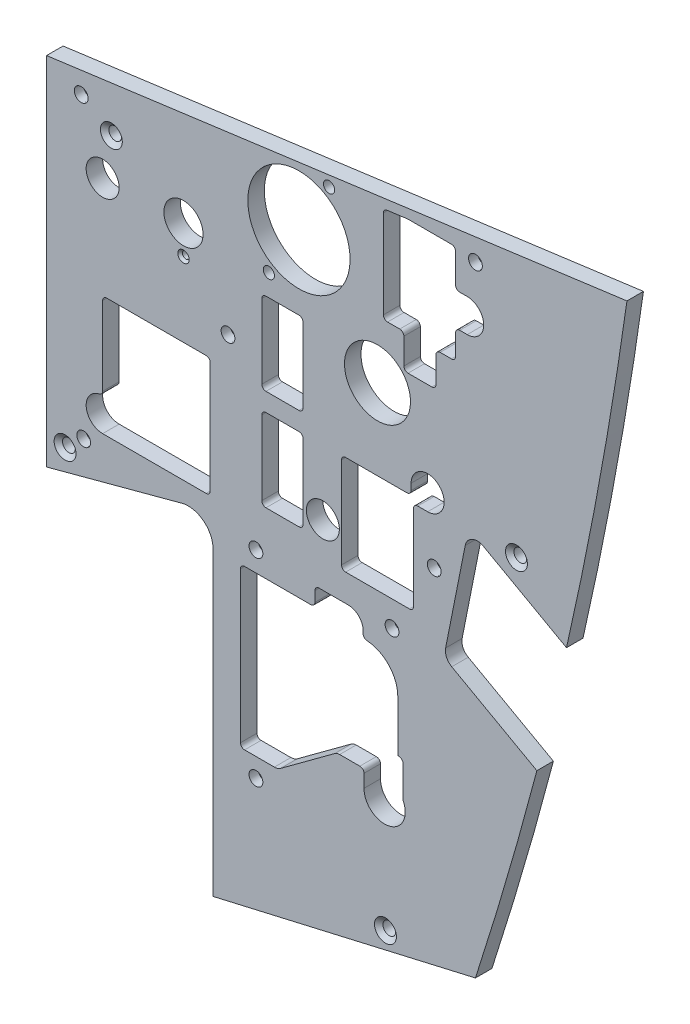
SolidWorks part; units mm, degrees
material "Acrylic (Medium-high impact)"
ref_plane "Front" through (0, 0, 0) normal (0, 0, 1) x (1, 0, 0)
ref_plane "Top" through (0, 0, 0) normal (0, 1, 0) x (1, 0, 0)
ref_plane "Right" through (0, 0, 0) normal (1, 0, 0) x (0, 0, -1)
sketch "Sketch1" plane through (0, 0, 0) normal (0, 0, 1) x (1, 0, 0)
  line L1 (3141.7988, 1080.7682) -> (3141.7988, 1063.3184)
  line L8 (3063.005, 1044.5596) -> (3063.005, 919.1617)
  line L9 (3063.005, 919.1617) -> (3164.2685, 942.5317)
  line L10 (3192.1789, 1037.6972) -> (3156.0776, 1057.8011)
  line L11 (3156.0776, 1057.8011) -> (3161.7423, 1086.3009)
  line L12 (3161.7423, 1086.3009) -> (3199.0539, 1065.5229)
  line L13 (3225.6026, 1207.3158) -> (2998.9238, 1176.9707)
  line L14 (2998.9238, 1176.9707) -> (2998.9238, 1039.8023)
  line L15 (2998.9238, 1039.8023) -> (3051.0147, 1053.76)
  line L16 (3063.005, 1044.5596) -> (3063.005, 919.1617)
  line L17 (3063.005, 919.1617) -> (3164.2685, 942.5317)
  line L18 (3192.1789, 1037.6972) -> (3156.0776, 1057.8011)
  line L19 (3156.0776, 1057.8011) -> (3161.7423, 1086.3009)
  line L20 (3161.7423, 1086.3009) -> (3199.0539, 1065.5229)
  line L21 (3225.6026, 1207.3158) -> (2998.9238, 1176.9707)
  line L22 (2998.9238, 1176.9707) -> (2998.9238, 1039.8023)
  line L23 (2998.9238, 1039.8023) -> (3051.0147, 1053.76)
  line L28 (3086.0872, 970.3576) -> (3119.75, 970.3576)
  line L29 (3085.0712, 977.1044) -> (3085.0712, 971.3736)
  line L30 (3074.5778, 981.8669) -> (3080.3087, 981.8669)
  line L31 (3073.5618, 1046.7322) -> (3073.5618, 982.8829)
  line L32 (3079.515, 1047.7482) -> (3074.5778, 1047.7482)
  line L33 (3084.2775, 1057.4478) -> (3084.2775, 1052.5107)
  line L34 (3125.3302, 1058.4638) -> (3085.2935, 1058.4638)
  line L35 (3126.3462, 1051.7169) -> (3126.3462, 1057.4478)
  line L36 (3136.8396, 1046.9544) -> (3131.1087, 1046.9544)
  line L37 (3137.8556, 988.4632) -> (3137.8556, 1045.9384)
  line L38 (3120.4684, 970.6551) -> (3137.558, 987.7447)
  line L39 (3086.0872, 970.3576) -> (3119.75, 970.3576)
  line L40 (3085.0712, 977.1044) -> (3085.0712, 971.3736)
  line L41 (3003.6862, 1145.6652) -> (3003.6863, 1063.3057)
  line L42 (3005.9087, 1147.2527) -> (3005.2737, 1147.2527)
  line L43 (3007.4962, 1162.696) -> (3007.4962, 1148.8402)
  line L44 (3012.2588, 1164.2835) -> (3009.0837, 1164.2835)
  line L45 (3018.6087, 1174.8809) -> (3018.6087, 1170.6476)
  line L46 (3036.8683, 1178.677) -> (3019.989, 1176.4548)
  line L47 (3031.8897, 1148.0185) -> (3038.6211, 1176.7408)
  line L48 (3037.8345, 1125.9265) -> (3031.9301, 1146.4148)
  line L49 (3060.8362, 1123.6307) -> (3040.8854, 1123.6307)
  line L50 (3062.4237, 1118.8682) -> (3062.4237, 1122.0432)
  line L51 (3075.1237, 1138.2357) -> (3075.1237, 1118.8682)
  line L52 (3108.2566, 1139.8232) -> (3076.7112, 1139.8232)
  line L53 (3126.5658, 1189.5696) -> (3111.2792, 1142.0263)
  line L54 (3155.879, 1194.3451) -> (3127.8699, 1190.6576)
  line L55 (3157.6737, 1190.6137) -> (3157.6737, 1192.7711)
  line L56 (3167.1987, 1184.2637) -> (3164.0237, 1184.2637)
  line L57 (3168.7862, 1148.0782) -> (3168.7862, 1182.6762)
  line L58 (3162.4362, 1146.4907) -> (3167.1987, 1146.4907)
  line L59 (3152.938, 1123.7744) -> (3156.193, 1141.3003)
  line L60 (3152.9113, 1088.7057) -> (3152.9113, 1123.4845)
  line L61 (3148.1488, 1087.1182) -> (3151.3238, 1087.1182)
  line L62 (3151.3238, 1074.4182) -> (3148.1488, 1074.4182)
  line L63 (3152.9113, 1063.3057) -> (3152.9113, 1072.8307)
  line L64 (3005.2738, 1061.7182) -> (3151.3238, 1061.7182)
  line L65 (3003.6862, 1145.6652) -> (3003.6863, 1063.3057)
  line L66 (3005.9087, 1147.2527) -> (3005.2737, 1147.2527)
  line L67 (3007.4962, 1162.696) -> (3007.4962, 1148.8402)
  line L68 (3012.2588, 1164.2835) -> (3009.0837, 1164.2835)
  line L69 (3018.6087, 1174.8809) -> (3018.6087, 1170.6476)
  line L70 (3036.8683, 1178.677) -> (3019.989, 1176.4548)
  line L71 (3031.8897, 1148.0185) -> (3038.6211, 1176.7408)
  line L72 (3037.8345, 1125.9265) -> (3031.9301, 1146.4148)
  line L73 (3060.8362, 1123.6307) -> (3040.8854, 1123.6307)
  line L74 (3062.4237, 1118.8682) -> (3062.4237, 1122.0432)
  line L75 (3075.1237, 1138.2357) -> (3075.1237, 1118.8682)
  line L76 (3108.2566, 1139.8232) -> (3076.7112, 1139.8232)
  line L77 (3126.5658, 1189.5696) -> (3111.2792, 1142.0263)
  line L78 (3155.879, 1194.3451) -> (3127.8699, 1190.6576)
  line L79 (3157.6737, 1190.6137) -> (3157.6737, 1192.7711)
  line L80 (3167.1987, 1184.2637) -> (3164.0237, 1184.2637)
  line L81 (3168.7862, 1148.0782) -> (3168.7862, 1182.6762)
  line L82 (3162.4362, 1146.4907) -> (3167.1987, 1146.4907)
  line L83 (3152.938, 1123.7744) -> (3156.193, 1141.3003)
  line L84 (3152.9113, 1088.7057) -> (3152.9113, 1123.4845)
  line L85 (3148.1488, 1087.1182) -> (3151.3238, 1087.1182)
  line L88 (3005.2738, 1061.7182) -> (3140.1986, 1061.7182)
  line L89 (3074.5778, 981.8669) -> (3080.3087, 981.8669)
  line L90 (3073.5618, 1046.7322) -> (3073.5618, 982.8829)
  line L91 (3079.515, 1047.7482) -> (3074.5778, 1047.7482)
  line L92 (3084.2775, 1057.4478) -> (3084.2775, 1052.5107)
  line L93 (3125.3302, 1058.4638) -> (3085.2935, 1058.4638)
  line L94 (3126.3462, 1051.7169) -> (3126.3462, 1057.4478)
  line L95 (3136.8396, 1046.9544) -> (3131.1087, 1046.9544)
  line L96 (3137.8556, 988.4632) -> (3137.8556, 1045.9384)
  line L97 (3120.4684, 970.6551) -> (3137.558, 987.7447)
  arc A0 (3141.7988, 1063.3184) -> (3140.1986, 1061.7182) centre (3140.1986, 1063.3184) cw
  arc A1 (3063.005, 1044.5596) -> (3051.0147, 1053.76) centre (3053.48, 1044.5596) ccw
  arc A2 (3063.005, 1044.5596) -> (3051.0147, 1053.76) centre (3053.48, 1044.5596) ccw
  arc A13 (3119.75, 970.3576) -> (3120.4684, 970.6551) centre (3119.75, 971.3736) ccw
  arc A14 (3085.0712, 971.3736) -> (3086.0872, 970.3576) centre (3086.0872, 971.3736) ccw
  arc A15 (3085.0712, 977.1044) -> (3080.3087, 981.8669) centre (3080.3087, 977.1044) ccw
  arc A16 (3073.5618, 982.8829) -> (3074.5778, 981.8669) centre (3074.5778, 982.8829) ccw
  arc A17 (3074.5778, 1047.7482) -> (3073.5618, 1046.7322) centre (3074.5778, 1046.7322) ccw
  arc A18 (3079.515, 1047.7482) -> (3084.2775, 1052.5107) centre (3079.515, 1052.5107) ccw
  arc A19 (3085.2935, 1058.4638) -> (3084.2775, 1057.4478) centre (3085.2935, 1057.4478) ccw
  arc A20 (3126.3462, 1057.4478) -> (3125.3302, 1058.4638) centre (3125.3302, 1057.4478) ccw
  arc A21 (3126.3462, 1051.7169) -> (3131.1087, 1046.9544) centre (3131.1087, 1051.7169) ccw
  arc A22 (3137.8556, 1045.9384) -> (3136.8396, 1046.9544) centre (3136.8396, 1045.9384) ccw
  arc A23 (3137.558, 987.7447) -> (3137.8556, 988.4632) centre (3136.8396, 988.4632) ccw
  arc A24 (3119.75, 970.3576) -> (3120.4684, 970.6551) centre (3119.75, 971.3736) ccw
  arc A25 (3085.0712, 971.3736) -> (3086.0872, 970.3576) centre (3086.0872, 971.3736) ccw
  arc A26 (3003.6863, 1063.3057) -> (3005.2738, 1061.7182) centre (3005.2738, 1063.3057) ccw
  arc A27 (3005.2737, 1147.2527) -> (3003.6862, 1145.6652) centre (3005.2737, 1145.6652) ccw
  arc A28 (3005.9087, 1147.2527) -> (3007.4962, 1148.8402) centre (3005.9087, 1148.8402) ccw
  arc A29 (3009.0837, 1164.2835) -> (3007.4962, 1162.696) centre (3009.0837, 1162.696) ccw
  arc A30 (3012.2588, 1164.2835) -> (3018.6087, 1170.6476) centre (3012.2588, 1170.6335) ccw
  arc A31 (3019.989, 1176.4548) -> (3018.6087, 1174.8809) centre (3020.1962, 1174.8809) ccw
  arc A32 (3038.6211, 1176.7408) -> (3036.8683, 1178.677) centre (3037.0755, 1177.1031) ccw
  arc A33 (3031.8897, 1148.0185) -> (3031.9301, 1146.4148) centre (3034.9809, 1147.294) ccw
  arc A34 (3037.8345, 1125.9265) -> (3040.8854, 1123.6307) centre (3040.8854, 1126.8057) ccw
  arc A35 (3062.4237, 1122.0432) -> (3060.8362, 1123.6307) centre (3060.8362, 1122.0432) ccw
  arc A36 (3062.4237, 1118.8682) -> (3075.1237, 1118.8682) centre (3068.7737, 1118.8682) ccw
  arc A37 (3076.7112, 1139.8232) -> (3075.1237, 1138.2357) centre (3076.7112, 1138.2357) ccw
  arc A38 (3108.2566, 1139.8232) -> (3111.2792, 1142.0263) centre (3108.2566, 1142.9982) ccw
  arc A39 (3127.8699, 1190.6576) -> (3126.5658, 1189.5696) centre (3128.0771, 1189.0837) ccw
  arc A40 (3157.6737, 1192.7711) -> (3155.879, 1194.3451) centre (3156.0862, 1192.7711) ccw
  arc A41 (3157.6737, 1190.6137) -> (3164.0237, 1184.2637) centre (3164.0237, 1190.6137) ccw
  arc A42 (3168.7862, 1182.6762) -> (3167.1987, 1184.2637) centre (3167.1987, 1182.6762) ccw
  arc A43 (3167.1987, 1146.4907) -> (3168.7862, 1148.0782) centre (3167.1987, 1148.0782) ccw
  arc A44 (3162.4362, 1146.4907) -> (3156.193, 1141.3003) centre (3162.4362, 1140.1407) ccw
  arc A45 (3152.938, 1123.7744) -> (3152.9113, 1123.4845) centre (3154.4988, 1123.4845) ccw
  arc A46 (3151.3238, 1087.1182) -> (3152.9113, 1088.7057) centre (3151.3238, 1088.7057) ccw
  arc A47 (3148.1488, 1087.1182) -> (3148.1488, 1074.4182) centre (3148.1488, 1080.7682) ccw
  arc A48 (3152.9113, 1072.8307) -> (3151.3238, 1074.4182) centre (3151.3238, 1072.8307) ccw
  arc A49 (3151.3238, 1061.7182) -> (3152.9113, 1063.3057) centre (3151.3238, 1063.3057) ccw
  arc A50 (3003.6863, 1063.3057) -> (3005.2738, 1061.7182) centre (3005.2738, 1063.3057) ccw
  arc A51 (3005.2737, 1147.2527) -> (3003.6862, 1145.6652) centre (3005.2737, 1145.6652) ccw
  arc A52 (3005.9087, 1147.2527) -> (3007.4962, 1148.8402) centre (3005.9087, 1148.8402) ccw
  arc A53 (3009.0837, 1164.2835) -> (3007.4962, 1162.696) centre (3009.0837, 1162.696) ccw
  arc A54 (3012.2588, 1164.2835) -> (3018.6087, 1170.6476) centre (3012.2588, 1170.6335) ccw
  arc A55 (3019.989, 1176.4548) -> (3018.6087, 1174.8809) centre (3020.1962, 1174.8809) ccw
  arc A56 (3038.6211, 1176.7408) -> (3036.8683, 1178.677) centre (3037.0755, 1177.1031) ccw
  arc A57 (3031.8897, 1148.0185) -> (3031.9301, 1146.4148) centre (3034.9809, 1147.294) ccw
  arc A58 (3037.8345, 1125.9265) -> (3040.8854, 1123.6307) centre (3040.8854, 1126.8057) ccw
  arc A59 (3062.4237, 1122.0432) -> (3060.8362, 1123.6307) centre (3060.8362, 1122.0432) ccw
  arc A60 (3062.4237, 1118.8682) -> (3075.1237, 1118.8682) centre (3068.7737, 1118.8682) ccw
  arc A61 (3076.7112, 1139.8232) -> (3075.1237, 1138.2357) centre (3076.7112, 1138.2357) ccw
  arc A62 (3108.2566, 1139.8232) -> (3111.2792, 1142.0263) centre (3108.2566, 1142.9982) ccw
  arc A63 (3127.8699, 1190.6576) -> (3126.5658, 1189.5696) centre (3128.0771, 1189.0837) ccw
  arc A64 (3157.6737, 1192.7711) -> (3155.879, 1194.3451) centre (3156.0862, 1192.7711) ccw
  arc A65 (3157.6737, 1190.6137) -> (3164.0237, 1184.2637) centre (3164.0237, 1190.6137) ccw
  arc A66 (3168.7862, 1182.6762) -> (3167.1987, 1184.2637) centre (3167.1987, 1182.6762) ccw
  arc A67 (3167.1987, 1146.4907) -> (3168.7862, 1148.0782) centre (3167.1987, 1148.0782) ccw
  arc A68 (3162.4362, 1146.4907) -> (3156.193, 1141.3003) centre (3162.4362, 1140.1407) ccw
  arc A69 (3152.938, 1123.7744) -> (3152.9113, 1123.4845) centre (3154.4988, 1123.4845) ccw
  arc A70 (3151.3238, 1087.1182) -> (3152.9113, 1088.7057) centre (3151.3238, 1088.7057) ccw
  arc A71 (3148.1488, 1087.1182) -> (3141.7988, 1080.7682) centre (3148.1488, 1080.7682) ccw
  arc A74 (3085.0712, 977.1044) -> (3080.3087, 981.8669) centre (3080.3087, 977.1044) ccw
  arc A75 (3073.5618, 982.8829) -> (3074.5778, 981.8669) centre (3074.5778, 982.8829) ccw
  arc A76 (3074.5778, 1047.7482) -> (3073.5618, 1046.7322) centre (3074.5778, 1046.7322) ccw
  arc A77 (3079.515, 1047.7482) -> (3084.2775, 1052.5107) centre (3079.515, 1052.5107) ccw
  arc A78 (3085.2935, 1058.4638) -> (3084.2775, 1057.4478) centre (3085.2935, 1057.4478) ccw
  arc A79 (3126.3462, 1057.4478) -> (3125.3302, 1058.4638) centre (3125.3302, 1057.4478) ccw
  arc A80 (3126.3462, 1051.7169) -> (3131.1087, 1046.9544) centre (3131.1087, 1051.7169) ccw
  arc A81 (3137.8556, 1045.9384) -> (3136.8396, 1046.9544) centre (3136.8396, 1045.9384) ccw
  arc A82 (3137.558, 987.7447) -> (3137.8556, 988.4632) centre (3136.8396, 988.4632) ccw
  spline S2 degree 3 poles (358.6348, -6517.1319) (3302.9174, 5219.504) (4321.4182, -3710.8351) (1858.1577, 8906.1513) knots -3.189525 -3.189525 -3.189525 -3.189525 3.135047 3.135047 3.135047 3.135047 only from (3164.2685, 942.5317) to (3192.1789, 1037.6972)
  spline S3 degree 3 poles (389.2582, -6395.5279) (3322.7867, 5208.463) (4321.6348, -3744.9341) (1825.6007, 9073.1269) knots -3.167547 -3.167547 -3.167547 -3.167547 3.16274 3.16274 3.16274 3.16274 only from (3199.0539, 1065.5229) to (3225.6026, 1207.3158)
  spline S4 degree 3 poles (3164.2685, 942.5317) (3174.5551, 973.7581) (3183.8621, 1005.3842) (3192.1789, 1037.6972) knots 0.073606 0.073606 0.073606 0.073606 0.193444 0.193444 0.193444 0.193444
  spline S5 degree 3 poles (3199.0539, 1065.5229) (3209.8343, 1111.0425) (3218.6934, 1158.0492) (3225.6026, 1207.3158) knots 0.227627 0.227627 0.227627 0.227627 0.394302 0.394302 0.394302 0.394302
  dimension "D4" = 1.6002
  dimension "D1" = 0
  dimension "D2" = 0
  dimension "D3" = 0
extrude "Boss-Extrude1" add sketch "Sketch1" against normal blind 6.35
sketch "Sketch2" plane through (0, 0, 0) normal (0, 0, 1) x (1, 0, 0)
  line L0 (3192.1789, 1037.6972) -> (3156.0776, 1057.8011) construction
  line L1 (3161.7423, 1086.3009) -> (3199.0539, 1065.5229) construction
  line L2 (3192.1789, 1037.6972) -> (3156.0776, 1057.8011)
  line L3 (3161.7423, 1086.3009) -> (3199.0539, 1065.5229)
  line L4 (3199.0669, 1079.6306) -> (3161.3537, 1100.6321)
  line L7 (3151.8624, 1052.8803) -> (3187.6652, 1032.9426)
  line L8 (3066.005, 917.3343) -> (3063.005, 916.642) construction
  line L9 (3156.0776, 1057.8011) -> (3161.7423, 1086.3009)
  line L11 (3151.8624, 1052.8803) -> (3161.3537, 1100.6321)
  line L13 (3063.005, 1044.5596) -> (3063.005, 919.1617) construction
  line L14 (3063.005, 919.1617) -> (3164.2685, 942.5317) construction
  line L15 (3063.005, 928.6867) -> (3063.005, 919.1617)
  line L16 (3063.005, 919.1617) -> (3164.2685, 942.5317)
  line L17 (3164.0169, 951.9986) -> (3063.005, 928.6867)
  line L18 (3225.6026, 1207.3158) -> (3222.335, 1206.8784)
  line L19 (3172.8694, 1200.2565) -> (3225.6062, 1207.3163) construction
  spline S0 degree 3 poles (2285.0986, -712.9269) (3195.8049, 1150.7322) (3504.2775, 619.5806) (3007.8793, 3191.2404) knots -1.489659 -1.489659 -1.489659 -1.489659 1.71614 1.71614 1.71614 1.71614 only from (3199.0539, 1065.5229) to (3225.6026, 1207.3158) construction
  spline S1 degree 3 poles (2230.4922, -826.0757) (3162.5298, 1129.2842) (3499.3421, 593.9621) (3039.8196, 3024.1358) knots -1.552909 -1.552909 -1.552909 -1.552909 1.644813 1.644813 1.644813 1.644813 only from (3164.2685, 942.5317) to (3192.1789, 1037.6972) construction
  spline S7 degree 3 poles (3164.2685, 942.5317) (3174.5551, 973.7581) (3183.8621, 1005.3842) (3192.1789, 1037.6972) knots 0.073606 0.073606 0.073606 0.073606 0.193444 0.193444 0.193444 0.193444
  spline S8 degree 3 poles (3199.0539, 1065.5229) (3209.8343, 1111.0425) (3218.6934, 1158.0492) (3225.6026, 1207.3158) knots 0.227627 0.227627 0.227627 0.227627 0.394302 0.394302 0.394302 0.394302
  spline S9 degree 1 poles (3161.2529, 943.5251) (3189.1041, 1038.4886) knots 0 0 1 1 construction
  spline S10 degree 3 poles (3161.2529, 943.5251) (3163.8211, 951.3213) (3168.8288, 966.9435) (3175.9775, 990.5676) (3181.627, 1010.4224) (3185.9604, 1026.4159) (3188.0683, 1034.4642) (3189.1041, 1038.4886) knots 0.073606 0.073606 0.073606 0.073606 0.103565 0.133525 0.163484 0.178464 0.193444 0.193444 0.193444 0.193444 only from (3164.0169, 951.9986) to (3187.6652, 1032.9426)
  spline S11 degree 1 poles (3195.9644, 1066.2546) (3222.4584, 1207.7568) knots 0 0 1 1 construction
  spline S12 degree 3 poles (3195.9644, 1066.2546) (3197.3128, 1071.9482) (3199.9368, 1083.3272) (3204.9583, 1106.3404) (3209.6153, 1129.6523) (3213.9117, 1153.3218) (3216.9524, 1171.2571) (3219.3354, 1186.3683) (3221.1497, 1198.5513) (3222.0285, 1204.6911) (3222.4584, 1207.7568) knots 0.227627 0.227627 0.227627 0.227627 0.248461 0.269296 0.310964 0.331799 0.352633 0.373467 0.383885 0.394302 0.394302 0.394302 0.394302 only from (3199.0669, 1079.6306) to (3222.335, 1206.8784)
  dimension "D1" = 12.3317
  dimension "D2" = 6.35
  dimension "D3" = 9.525
  dimension "D4" = 3.175
  dimension "D5" = 3.175
extrude "Cut-Extrude1" cut sketch "Sketch2" against normal through all
sketch "Sketch16" plane through (0, 0, -6.35) normal (0, 0, -1) x (-1, 0, 0)
  circle A0 centre (-3096.0788, 1167.4457) radius 19.685
  dimension "D1" = 39.37
extrude "Cut-Extrude2" cut sketch "Sketch16" against normal through all
hole_wizard "Hole1" positions "Sketch4" profile "Sketch5" legacy
sketch "Sketch4" plane through (0, 0, 0) normal (0, 0, 1) x (1, 0, 0)
  point P0 (3164.0237, 1190.6137)
  point P2 (3068.7737, 1118.8682)
  point P4 (3148.1488, 1080.7682)
  point P6 (3012.2588, 1170.6335)
  point P8 (3013.2113, 1056.3207)
  point P10 (3131.9025, 1052.5107)
  point P12 (3079.515, 1052.5107)
  point P14 (3079.515, 976.3107)
sketch "Sketch5" plane through (3164.0237, 1190.6137, 0) normal (1, 0, 0) x (0, -1, 0)
  line L0 (0, 0) -> (0, 3.429)
  line L1 (0, 3.429) -> (2.5273, 3.429)
  line L2 (2.5273, 3.429) -> (2.6543, 0)
  line L3 (2.6543, 0) -> (0, 0)
  line L4 (0, 110) -> (0, -10) construction
  dimension "Minor Diameter" = 5.0546
  dimension "Depth" = 3.429
  dimension "Major Diameter" = 5.3086
hole_wizard "#6 Clearance Hole1" positions "Sketch6" profile "Sketch7" hole size "#6" standard "ANSI Inch" end condition through all
sketch "Sketch6" plane through (0, 0, 0) normal (0, 0, 1) x (1, 0, 0)
  point P0 (3079.515, 976.3107)
  point P3 (3079.515, 1052.5107)
  point P6 (3131.9025, 1052.5107)
  point P9 (3013.2113, 1056.3207)
  point P12 (3012.2588, 1170.6335)
  point P15 (3068.7737, 1118.8682)
  point P18 (3148.1488, 1080.7682)
  point P21 (3164.0237, 1190.6137)
  point P24 (3107.6675, 1187.518)
  point P27 (3084.49, 1147.3734)
sketch "Sketch7" plane through (3079.515, 976.3107, 0) normal (1, 0, 0) x (0, -1, 0)
  line L0 (0, 0) -> (0, 6.35)
  line L1 (0, 6.35) -> (2.1526, 6.35)
  line L2 (2.1526, 6.35) -> (2.1526, 0)
  line L5 (2.1526, 0) -> (0, 0)
  line L11 (0, -6.35) -> (0, 107.95) construction
  dimension "Thru Hole Dia." = 4.3053
  dimension "Thru Hole Depth" = 6.35
sketch "Sketch8" plane through (0, 0, -6.35) normal (0, 0, -1) x (-1, 0, 0)
  line L0 (-3020.5138, 1074.4182) -> (-3020.5138, 1107.6816)
  line L1 (-3020.5138, 1107.6816) -> (-3061.927, 1107.6816)
  line L2 (-3061.927, 1107.6816) -> (-3061.927, 1061.7182)
  line L3 (-3061.927, 1061.7182) -> (-3020.5138, 1061.7182)
  line L6 (-3156.379, 1191.9882) -> (-3128.5884, 1191.9882)
  line L7 (-3097.6663, 1100.1857) -> (-3081.7913, 1100.1857)
  line L8 (-3097.6663, 1138.9977) -> (-3081.7913, 1138.9977)
  line L9 (-3097.6663, 1138.9977) -> (-3097.6663, 1107.2477)
  line L10 (-3097.6663, 1107.2477) -> (-3081.7913, 1107.2477)
  line L11 (-3081.7913, 1138.9977) -> (-3081.7913, 1107.2477)
  line L12 (-3097.6663, 1138.9977) -> (-3081.7913, 1107.2477) construction
  line L13 (-3097.6663, 1107.2477) -> (-3081.7913, 1138.9977) construction
  line L14 (-3097.6663, 1100.1857) -> (-3097.6663, 1068.4357)
  line L15 (-3097.6663, 1068.4357) -> (-3081.7913, 1068.4357)
  line L16 (-3081.7913, 1100.1857) -> (-3081.7913, 1068.4357)
  line L17 (-3097.6663, 1100.1857) -> (-3081.7913, 1068.4357) construction
  line L18 (-3097.6663, 1068.4357) -> (-3081.7913, 1100.1857) construction
  line L19 (-3154.7915, 1190.4007) -> (-3130.1759, 1190.4007) construction
  line L20 (-3154.7915, 1190.4007) -> (-3154.7915, 1155.3585) construction
  line L21 (-3154.7915, 1155.3585) -> (-3130.1759, 1155.3585) construction
  line L22 (-3130.1759, 1190.4007) -> (-3130.1759, 1155.3585) construction
  line L23 (-3154.7915, 1190.4007) -> (-3130.1759, 1155.3585) construction
  line L24 (-3154.7915, 1155.3585) -> (-3130.1759, 1190.4007) construction
  line L25 (-3128.5884, 1191.9882) -> (-3128.5884, 1153.771)
  line L26 (-3156.379, 1153.771) -> (-3148.8245, 1153.771)
  line L27 (-3156.379, 1191.9882) -> (-3156.379, 1177.6057)
  line L28 (-3160.8488, 1177.6057) -> (-3156.379, 1177.6057)
  line L29 (-3160.8488, 1164.9057) -> (-3156.379, 1164.9057)
  line L30 (-3156.379, 1164.9057) -> (-3156.379, 1153.771)
  line L31 (-3156.379, 1191.9882) -> (-3156.379, 1153.771) construction
  line L32 (-3140.2001, 1062.3311) -> (-3112.4595, 1062.3311)
  line L33 (-3138.6126, 1098.9607) -> (-3114.047, 1098.9607) construction
  line L34 (-3138.6126, 1098.9607) -> (-3138.6126, 1063.9186) construction
  line L35 (-3138.6126, 1063.9186) -> (-3114.047, 1063.9186) construction
  line L36 (-3114.047, 1098.9607) -> (-3114.047, 1063.9186) construction
  line L37 (-3138.6126, 1098.9607) -> (-3114.047, 1063.9186) construction
  line L38 (-3138.6126, 1063.9186) -> (-3114.047, 1098.9607) construction
  line L39 (-3112.4595, 1100.5482) -> (-3112.4595, 1062.3311)
  line L40 (-3139.2588, 1100.5482) -> (-3112.4595, 1100.5482)
  line L41 (-3140.2001, 1098.2307) -> (-3140.2001, 1062.3311)
  line L42 (-3139.2588, 1104.5807) -> (-3139.2588, 1100.5482)
  line L43 (-3145.6088, 1098.2307) -> (-3140.2001, 1098.2307)
  line L44 (-3140.2001, 1100.5482) -> (-3140.2001, 1062.3311) construction
  line L45 (-3140.2001, 1100.5482) -> (-3112.4595, 1100.5482) construction
  line L70 (-3005.2738, 1061.7182) -> (-3020.5138, 1061.7182)
  line L71 (-3020.5138, 1061.7182) -> (-3061.927, 1061.7182)
  line L72 (-3061.927, 1061.7182) -> (-3140.1986, 1061.7182)
  line L73 (-3136.4697, 1153.771) -> (-3136.4697, 1140.6386)
  line L74 (-3136.4697, 1140.6386) -> (-3148.8245, 1140.6386)
  line L75 (-3148.8245, 1140.6386) -> (-3148.8245, 1153.771)
  line L76 (-3136.4697, 1153.771) -> (-3128.5884, 1153.771)
  line L77 (-3156.379, 1153.771) -> (-3128.5884, 1153.771) construction
  line L93 (-3141.7988, 1080.7682) -> (-3141.7988, 1063.3184)
  line L94 (-3151.3238, 1087.1182) -> (-3148.1488, 1087.1182)
  line L95 (-3152.9113, 1123.4845) -> (-3152.9113, 1088.7057)
  line L96 (-3156.193, 1141.3003) -> (-3152.938, 1123.7744)
  line L97 (-3167.1987, 1146.4907) -> (-3162.4362, 1146.4907)
  line L98 (-3168.7862, 1182.6762) -> (-3168.7862, 1148.0782)
  line L99 (-3164.0237, 1184.2637) -> (-3167.1987, 1184.2637)
  line L100 (-3157.6737, 1192.7711) -> (-3157.6737, 1190.6137)
  line L101 (-3127.8699, 1190.6576) -> (-3155.879, 1194.3451)
  line L102 (-3111.2792, 1142.0263) -> (-3126.5658, 1189.5696)
  line L103 (-3076.7112, 1139.8232) -> (-3108.2566, 1139.8232)
  line L104 (-3075.1237, 1118.8682) -> (-3075.1237, 1138.2357)
  line L105 (-3062.4237, 1122.0432) -> (-3062.4237, 1118.8682)
  line L106 (-3040.8854, 1123.6307) -> (-3060.8362, 1123.6307)
  line L107 (-3031.9301, 1146.4148) -> (-3037.8345, 1125.9265)
  line L108 (-3038.6211, 1176.7408) -> (-3031.8897, 1148.0185)
  line L109 (-3019.989, 1176.4548) -> (-3036.8683, 1178.677)
  line L110 (-3018.6087, 1170.6476) -> (-3018.6087, 1174.8809)
  line L111 (-3009.0837, 1164.2835) -> (-3012.2588, 1164.2835)
  line L112 (-3007.4962, 1148.8402) -> (-3007.4962, 1162.696)
  line L113 (-3005.2737, 1147.2527) -> (-3005.9087, 1147.2527)
  line L114 (-3003.6863, 1063.3057) -> (-3003.6862, 1145.6652)
  line L115 (-3140.1986, 1061.7182) -> (-3005.2738, 1061.7182)
  line L116 (-3141.7988, 1080.7682) -> (-3141.7988, 1063.3184)
  line L117 (-3151.3238, 1087.1182) -> (-3148.1488, 1087.1182)
  line L118 (-3152.9113, 1123.4845) -> (-3152.9113, 1088.7057)
  line L119 (-3156.193, 1141.3003) -> (-3152.938, 1123.7744)
  line L120 (-3167.1987, 1146.4907) -> (-3162.4362, 1146.4907)
  line L121 (-3168.7862, 1182.6762) -> (-3168.7862, 1148.0782)
  line L122 (-3164.0237, 1184.2637) -> (-3167.1987, 1184.2637)
  line L123 (-3157.6737, 1192.7711) -> (-3157.6737, 1190.6137)
  line L124 (-3127.8699, 1190.6576) -> (-3155.879, 1194.3451)
  line L125 (-3111.2792, 1142.0263) -> (-3126.5658, 1189.5696)
  line L126 (-3076.7112, 1139.8232) -> (-3108.2566, 1139.8232)
  line L127 (-3075.1237, 1118.8682) -> (-3075.1237, 1138.2357)
  line L128 (-3062.4237, 1122.0432) -> (-3062.4237, 1118.8682)
  line L129 (-3040.8854, 1123.6307) -> (-3060.8362, 1123.6307)
  line L130 (-3031.9301, 1146.4148) -> (-3037.8345, 1125.9265)
  line L131 (-3038.6211, 1176.7408) -> (-3031.8897, 1148.0185)
  line L132 (-3019.989, 1176.4548) -> (-3036.8683, 1178.677)
  line L133 (-3018.6087, 1170.6476) -> (-3018.6087, 1174.8809)
  line L134 (-3009.0837, 1164.2835) -> (-3012.2588, 1164.2835)
  line L135 (-3007.4962, 1148.8402) -> (-3007.4962, 1162.696)
  line L136 (-3005.2737, 1147.2527) -> (-3005.9087, 1147.2527)
  line L137 (-3003.6863, 1063.3057) -> (-3003.6862, 1145.6652)
  circle A0 centre (-3020.5137, 1146.8717) radius 6.35
  arc A2 (-3139.2588, 1104.5807) -> (-3145.6088, 1098.2307) centre (-3145.6088, 1104.5807) ccw
  circle A3 centre (-3105.2863, 1075.3707) radius 6.35
  arc A4 (-3020.5138, 1061.7182) -> (-3020.5138, 1074.4182) centre (-3020.5138, 1068.0682) ccw
  circle A5 centre (-3126.3048, 1131.5682) radius 12.7
  arc A6 (-3160.8488, 1177.6057) -> (-3160.8488, 1164.9057) centre (-3160.8488, 1171.2557) ccw
  arc A30 (-3141.7988, 1080.7682) -> (-3148.1488, 1087.1182) centre (-3148.1488, 1080.7682) ccw
  arc A31 (-3152.9113, 1088.7057) -> (-3151.3238, 1087.1182) centre (-3151.3238, 1088.7057) ccw
  arc A32 (-3152.9113, 1123.4845) -> (-3152.938, 1123.7744) centre (-3154.4988, 1123.4845) ccw
  arc A33 (-3156.193, 1141.3003) -> (-3162.4362, 1146.4907) centre (-3162.4362, 1140.1407) ccw
  arc A34 (-3168.7862, 1148.0782) -> (-3167.1987, 1146.4907) centre (-3167.1987, 1148.0782) ccw
  arc A35 (-3167.1987, 1184.2637) -> (-3168.7862, 1182.6762) centre (-3167.1987, 1182.6762) ccw
  arc A36 (-3164.0237, 1184.2637) -> (-3157.6737, 1190.6137) centre (-3164.0237, 1190.6137) ccw
  arc A37 (-3155.879, 1194.3451) -> (-3157.6737, 1192.7711) centre (-3156.0862, 1192.7711) ccw
  arc A38 (-3126.5658, 1189.5696) -> (-3127.8699, 1190.6576) centre (-3128.0771, 1189.0837) ccw
  arc A39 (-3111.2792, 1142.0263) -> (-3108.2566, 1139.8232) centre (-3108.2566, 1142.9982) ccw
  arc A40 (-3075.1237, 1138.2357) -> (-3076.7112, 1139.8232) centre (-3076.7112, 1138.2357) ccw
  arc A41 (-3075.1237, 1118.8682) -> (-3062.4237, 1118.8682) centre (-3068.7737, 1118.8682) ccw
  arc A42 (-3060.8362, 1123.6307) -> (-3062.4237, 1122.0432) centre (-3060.8362, 1122.0432) ccw
  arc A43 (-3040.8854, 1123.6307) -> (-3037.8345, 1125.9265) centre (-3040.8854, 1126.8057) ccw
  arc A44 (-3031.9301, 1146.4148) -> (-3031.8897, 1148.0185) centre (-3034.9809, 1147.294) ccw
  arc A45 (-3036.8683, 1178.677) -> (-3038.6211, 1176.7408) centre (-3037.0755, 1177.1031) ccw
  arc A69 (-3018.6087, 1174.8809) -> (-3019.989, 1176.4548) centre (-3020.1962, 1174.8809) ccw
  arc A70 (-3018.6087, 1170.6476) -> (-3012.2588, 1164.2835) centre (-3012.2588, 1170.6335) ccw
  arc A71 (-3007.4962, 1162.696) -> (-3009.0837, 1164.2835) centre (-3009.0837, 1162.696) ccw
  arc A72 (-3007.4962, 1148.8402) -> (-3005.9087, 1147.2527) centre (-3005.9087, 1148.8402) ccw
  arc A73 (-3003.6862, 1145.6652) -> (-3005.2737, 1147.2527) centre (-3005.2737, 1145.6652) ccw
  arc A74 (-3005.2738, 1061.7182) -> (-3003.6863, 1063.3057) centre (-3005.2738, 1063.3057) ccw
  arc A75 (-3141.7988, 1063.3184) -> (-3140.1986, 1061.7182) centre (-3140.1986, 1063.3184) ccw
  arc A76 (-3141.7988, 1080.7682) -> (-3148.1488, 1087.1182) centre (-3148.1488, 1080.7682) ccw
  arc A77 (-3152.9113, 1088.7057) -> (-3151.3238, 1087.1182) centre (-3151.3238, 1088.7057) ccw
  arc A78 (-3152.9113, 1123.4845) -> (-3152.938, 1123.7744) centre (-3154.4988, 1123.4845) ccw
  arc A79 (-3156.193, 1141.3003) -> (-3162.4362, 1146.4907) centre (-3162.4362, 1140.1407) ccw
  arc A80 (-3168.7862, 1148.0782) -> (-3167.1987, 1146.4907) centre (-3167.1987, 1148.0782) ccw
  arc A81 (-3167.1987, 1184.2637) -> (-3168.7862, 1182.6762) centre (-3167.1987, 1182.6762) ccw
  arc A82 (-3164.0237, 1184.2637) -> (-3157.6737, 1190.6137) centre (-3164.0237, 1190.6137) ccw
  arc A83 (-3155.879, 1194.3451) -> (-3157.6737, 1192.7711) centre (-3156.0862, 1192.7711) ccw
  arc A84 (-3126.5658, 1189.5696) -> (-3127.8699, 1190.6576) centre (-3128.0771, 1189.0837) ccw
  arc A85 (-3111.2792, 1142.0263) -> (-3108.2566, 1139.8232) centre (-3108.2566, 1142.9982) ccw
  arc A86 (-3075.1237, 1138.2357) -> (-3076.7112, 1139.8232) centre (-3076.7112, 1138.2357) ccw
  arc A87 (-3075.1237, 1118.8682) -> (-3062.4237, 1118.8682) centre (-3068.7737, 1118.8682) ccw
  arc A88 (-3060.8362, 1123.6307) -> (-3062.4237, 1122.0432) centre (-3060.8362, 1122.0432) ccw
  arc A89 (-3040.8854, 1123.6307) -> (-3037.8345, 1125.9265) centre (-3040.8854, 1126.8057) ccw
  arc A90 (-3031.9301, 1146.4148) -> (-3031.8897, 1148.0185) centre (-3034.9809, 1147.294) ccw
  arc A91 (-3036.8683, 1178.677) -> (-3038.6211, 1176.7408) centre (-3037.0755, 1177.1031) ccw
  arc A92 (-3018.6087, 1174.8809) -> (-3019.989, 1176.4548) centre (-3020.1962, 1174.8809) ccw
  arc A93 (-3018.6087, 1170.6476) -> (-3012.2588, 1164.2835) centre (-3012.2588, 1170.6335) ccw
  arc A94 (-3007.4962, 1162.696) -> (-3009.0837, 1164.2835) centre (-3009.0837, 1162.696) ccw
  arc A95 (-3007.4962, 1148.8402) -> (-3005.9087, 1147.2527) centre (-3005.9087, 1148.8402) ccw
  arc A96 (-3003.6862, 1145.6652) -> (-3005.2737, 1147.2527) centre (-3005.2737, 1145.6652) ccw
  arc A97 (-3005.2738, 1061.7182) -> (-3003.6863, 1063.3057) centre (-3005.2738, 1063.3057) ccw
  arc A98 (-3141.7988, 1063.3184) -> (-3140.1986, 1061.7182) centre (-3140.1986, 1063.3184) ccw
  point P5 (-3142.4837, 1172.8796)
  point P9 (-3126.3298, 1081.4396)
  point P12 (-3089.7288, 1084.3107)
  point P13 (-3089.7288, 1123.1227)
  dimension "D2" = 1.5875
  dimension "D3" = 0
  dimension "D1" = 1.5875
extrude "Boss-Extrude4" add sketch "Sketch8" against normal up to surface (6.35 mm away) contours L116 A98 L72 L2 L1 L0 A4 L70 A97 L137 A96 L136 A95 L135 A94 L134 A93 L133 A92 L132 A91 L131 A90 L130 A89 L129 A88 L128 A87 L127 A86 L126 A85 L125 A84 L124 L25 L26 L30 L29 A6 L28 L27 L6 A83 L123 A82 L122 A81 L121
sketch "Sketch9" plane through (0, 0, -6.35) normal (0, 0, -1) x (-1, 0, 0)
  line L0 (-3121.1075, 1000.3713) -> (-3111.7511, 1000.3713)
  line L1 (-3121.1075, 993.7732) -> (-3121.1075, 1000.3713)
  line L12 (-3119.75, 970.3576) -> (-3086.0872, 970.3576)
  line L13 (-3137.558, 987.7447) -> (-3120.4684, 970.6551)
  line L14 (-3137.8556, 1045.9384) -> (-3137.8556, 988.4632)
  line L15 (-3131.1087, 1046.9544) -> (-3136.8396, 1046.9544)
  line L16 (-3126.3462, 1057.4478) -> (-3126.3462, 1051.7169)
  line L17 (-3085.2935, 1058.4638) -> (-3125.3302, 1058.4638)
  line L18 (-3084.2775, 1052.5107) -> (-3084.2775, 1057.4478)
  line L19 (-3074.5778, 1047.7482) -> (-3079.515, 1047.7482)
  line L20 (-3073.5618, 982.8829) -> (-3073.5618, 1046.7322)
  line L21 (-3080.3087, 981.8669) -> (-3074.5778, 981.8669)
  line L22 (-3085.0712, 971.3736) -> (-3085.0712, 977.1044)
  line L23 (-3119.75, 970.3576) -> (-3086.0872, 970.3576)
  line L24 (-3137.558, 987.7447) -> (-3120.4684, 970.6551)
  line L25 (-3137.8556, 1045.9384) -> (-3137.8556, 988.4632)
  line L26 (-3131.1087, 1046.9544) -> (-3136.8396, 1046.9544)
  line L27 (-3126.3462, 1057.4478) -> (-3126.3462, 1051.7169)
  line L28 (-3085.2935, 1058.4638) -> (-3125.3302, 1058.4638)
  line L29 (-3084.2775, 1052.5107) -> (-3084.2775, 1057.4478)
  line L30 (-3074.5778, 1047.7482) -> (-3079.515, 1047.7482)
  line L31 (-3073.5618, 982.8829) -> (-3073.5618, 1046.7322)
  line L32 (-3080.3087, 981.8669) -> (-3074.5778, 981.8669)
  line L33 (-3085.0712, 971.3736) -> (-3085.0712, 977.1044)
  line L49 (-3082.182, 1044.7712) -> (-3102.248, 1044.7712)
  line L50 (-3120.79, 1046.1607) -> (-3120.79, 1043.6048)
  line L51 (-3134.125, 1030.9207) -> (-3134.125, 1011.1663)
  line L62 (-3072.657, 1044.7712) -> (-3082.182, 1044.7712)
  line L63 (-3072.657, 983.6132) -> (-3072.657, 1044.7712)
  line L64 (-3086.6174, 983.6132) -> (-3072.657, 983.6132)
  line L65 (-3109.8672, 999.752) -> (-3089.0666, 984.4183)
  line L67 (-3136.1316, 1011.1663) -> (-3136.1316, 997.3487)
  line L68 (-3134.125, 1011.1663) -> (-3136.1316, 1011.1663)
  line L71 (-3102.248, 1051.8757) -> (-3115.075, 1051.8757)
  line L72 (-3102.248, 1044.7712) -> (-3102.248, 1051.8757)
  arc A0 (-3136.1316, 997.3487) -> (-3121.1075, 993.7732) centre (-3129.045, 993.7732) ccw
  arc A12 (-3120.4684, 970.6551) -> (-3119.75, 970.3576) centre (-3119.75, 971.3736) ccw
  arc A13 (-3137.8556, 988.4632) -> (-3137.558, 987.7447) centre (-3136.8396, 988.4632) ccw
  arc A14 (-3136.8396, 1046.9544) -> (-3137.8556, 1045.9384) centre (-3136.8396, 1045.9384) ccw
  arc A15 (-3131.1087, 1046.9544) -> (-3126.3462, 1051.7169) centre (-3131.1087, 1051.7169) ccw
  arc A16 (-3125.3302, 1058.4638) -> (-3126.3462, 1057.4478) centre (-3125.3302, 1057.4478) ccw
  arc A17 (-3084.2775, 1057.4478) -> (-3085.2935, 1058.4638) centre (-3085.2935, 1057.4478) ccw
  arc A18 (-3084.2775, 1052.5107) -> (-3079.515, 1047.7482) centre (-3079.515, 1052.5107) ccw
  arc A19 (-3073.5618, 1046.7322) -> (-3074.5778, 1047.7482) centre (-3074.5778, 1046.7322) ccw
  arc A20 (-3074.5778, 981.8669) -> (-3073.5618, 982.8829) centre (-3074.5778, 982.8829) ccw
  arc A21 (-3080.3087, 981.8669) -> (-3085.0712, 977.1044) centre (-3080.3087, 977.1044) ccw
  arc A22 (-3086.0872, 970.3576) -> (-3085.0712, 971.3736) centre (-3086.0872, 971.3736) ccw
  arc A23 (-3120.4684, 970.6551) -> (-3119.75, 970.3576) centre (-3119.75, 971.3736) ccw
  arc A24 (-3137.8556, 988.4632) -> (-3137.558, 987.7447) centre (-3136.8396, 988.4632) ccw
  arc A25 (-3136.8396, 1046.9544) -> (-3137.8556, 1045.9384) centre (-3136.8396, 1045.9384) ccw
  arc A26 (-3131.1087, 1046.9544) -> (-3126.3462, 1051.7169) centre (-3131.1087, 1051.7169) ccw
  arc A27 (-3125.3302, 1058.4638) -> (-3126.3462, 1057.4478) centre (-3125.3302, 1057.4478) ccw
  arc A28 (-3084.2775, 1057.4478) -> (-3085.2935, 1058.4638) centre (-3085.2935, 1057.4478) ccw
  arc A29 (-3084.2775, 1052.5107) -> (-3079.515, 1047.7482) centre (-3079.515, 1052.5107) ccw
  arc A30 (-3073.5618, 1046.7322) -> (-3074.5778, 1047.7482) centre (-3074.5778, 1046.7322) ccw
  arc A31 (-3074.5778, 981.8669) -> (-3073.5618, 982.8829) centre (-3074.5778, 982.8829) ccw
  arc A32 (-3080.3087, 981.8669) -> (-3085.0712, 977.1044) centre (-3080.3087, 977.1044) ccw
  arc A33 (-3086.0872, 970.3576) -> (-3085.0712, 971.3736) centre (-3086.0872, 971.3736) ccw
  arc A39 (-3120.79, 1043.6048) -> (-3134.125, 1030.9207) centre (-3121.425, 1030.9207) ccw
  arc A48 (-3089.0666, 984.4183) -> (-3086.6174, 983.6132) centre (-3086.6174, 987.7407) ccw
  arc A49 (-3109.8672, 999.752) -> (-3111.7511, 1000.3713) centre (-3111.7511, 997.1963) ccw
  arc A52 (-3115.075, 1051.8757) -> (-3120.79, 1046.1607) centre (-3115.075, 1046.1607) ccw
  dimension "D1" = 0
extrude "Boss-Extrude5" add sketch "Sketch9" against normal up to surface (6.35 mm away) up to face at (3035.809, 1082.6436, 0)
fillet "Fillet1" radius 1.5875 36 edges at (3136.1316, 1011.1663, -3.175) (3120.79, 1043.6048, -3.175) (3073.5618, 1044.7712, -3.175) (3102.248, 1044.7712, -3.175) (3102.248, 1051.8757, -3.175) (3140.2001, 1062.3311, -3.175) (3112.4595, 1062.3311, -3.175) (3112.4595, 1100.5482, -3.175) (3140.2001, 1098.2307, -3.175) (3139.2588, 1100.5482, -3.175) (3156.379, 1164.9057, -3.175) (3156.379, 1177.6057, -3.175) (3156.379, 1191.9882, -3.175) (3137.9769, 1191.9882, -3.175) (3128.5884, 1190.7522, -3.175) (3128.5884, 1153.771, -3.175) (3156.379, 1153.771, -3.175) (3148.8245, 1140.6386, -3.175) (3136.4697, 1140.6386, -3.175) (3148.8245, 1153.771, -3.175) (3136.4697, 1153.771, -3.175) (3097.6663, 1138.9977, -3.175) (3081.7913, 1138.9977, -3.175) (3081.7913, 1107.2477, -3.175) (3097.6663, 1107.2477, -3.175) (3097.6663, 1100.1857, -3.175) (3097.6663, 1068.4357, -3.175) (3081.7913, 1068.4357, -3.175) (3081.7913, 1100.1857, -3.175) (3061.927, 1107.6816, -3.175) (3061.927, 1061.7182, -3.175) (3020.5138, 1074.4182, -3.175) (3020.5138, 1107.6816, -3.175) (3136.1316, 997.3487, -3.175) (3121.1075, 1000.3713, -3.175) (3073.5618, 983.6132, -3.175)
fillet "Fillet2" radius 4.7625 2 edges at (3151.8624, 1052.8803, -3.175) (3161.3537, 1100.6321, -3.175)
hole_wizard "CSK for #8 Flat Head Machine Screw (100)" positions "Sketch10" profile "Sketch11" countersink size "#8" standard "ANSI Inch"
sketch "Sketch10" plane through (0, 0, 0) normal (0, 0, 1) x (1, 0, 0)
  line L4 (3097.8947, 943.175) -> (3160.8673, 957.8693) construction
  point P0 (3129.381, 950.5221)
  point P23 (3179.8051, 1100.0455)
  point P33 (3023.8644, 1162.7467)
  point P37 (3006.0464, 1049.8882)
sketch "Sketch11" plane through (3129.381, 950.5221, 0) normal (1, 0, 0) x (0, -1, 0)
  line L0 (0, 0) -> (0, 7.8256)
  line L1 (0, 7.8256) -> (2.4574, 6.349)
  line L2 (2.4574, 6.349) -> (2.4574, 1.4759)
  line L3 (2.4574, 1.4759) -> (4.2164, 0)
  line L4 (4.2164, 0) -> (0, 0)
  line L5 (-2.4574, 1.4759) -> (-4.2164, 0) construction
  line L6 (0, 7.8256) -> (-2.4575, 6.349) construction
  line L7 (0, -6.35) -> (0, 107.95) construction
  dimension "Hole Dia." = 4.9149
  dimension "Hole Depth" = 6.349
  dimension "Near C'Sink Dia." = 8.4328
  dimension "Near C'Sink Angle" = 100
  dimension "Drill Angle" = 118
hole_wizard "9/16 Clearance Hole1" positions "Sketch12" profile "Sketch13" hole size "9/16" standard "ANSI Inch" end condition through all
sketch "Sketch12" plane through (0, 0, 0) normal (0, 0, 1) x (1, 0, 0)
  point P1 (3051.6288, 1147.4432)
sketch "Sketch13" plane through (3051.6288, 1147.4432, 0) normal (1, 0, 0) x (0, -1, 0)
  line L0 (0, 0) -> (0, 6.35)
  line L1 (0, 6.35) -> (7.54, 6.35)
  line L2 (7.54, 6.35) -> (7.54, 0)
  line L5 (7.54, 0) -> (0, 0)
  line L11 (0, -6.35) -> (0, 107.95) construction
  dimension "Thru Hole Dia." = 15.08
  dimension "Thru Hole Depth" = 6.35
hole_wizard "CSK for #2 Flat Head Machine Screw1" positions "Sketch14" profile "Sketch15" countersink size "#2" standard "ANSI Inch" end condition through all
sketch "Sketch14" plane through (0, 0, 0) normal (0, 0, 1) x (1, 0, 0)
  point P0 (3051.6288, 1136.3307)
sketch "Sketch15" plane through (3051.6288, 1136.3307, 0) normal (1, 0, 0) x (0, -1, 0)
  line L0 (0, 0) -> (0, 6.35)
  line L1 (0, 6.35) -> (1.3525, 6.35)
  line L2 (1.3525, 6.35) -> (1.3525, 0.9569)
  line L3 (1.3525, 0.9569) -> (2.1844, 0)
  line L5 (2.1844, 0) -> (0, 0)
  line L6 (-1.3525, 0.9569) -> (-2.1844, 0) construction
  line L11 (0, -6.35) -> (0, 107.95) construction
  dimension "Thru Hole Dia." = 2.7051
  dimension "Thru Hole Depth" = 6.35
  dimension "Near C'Sink Dia." = 4.3688
  dimension "Near C'Sink Angle" = 82
